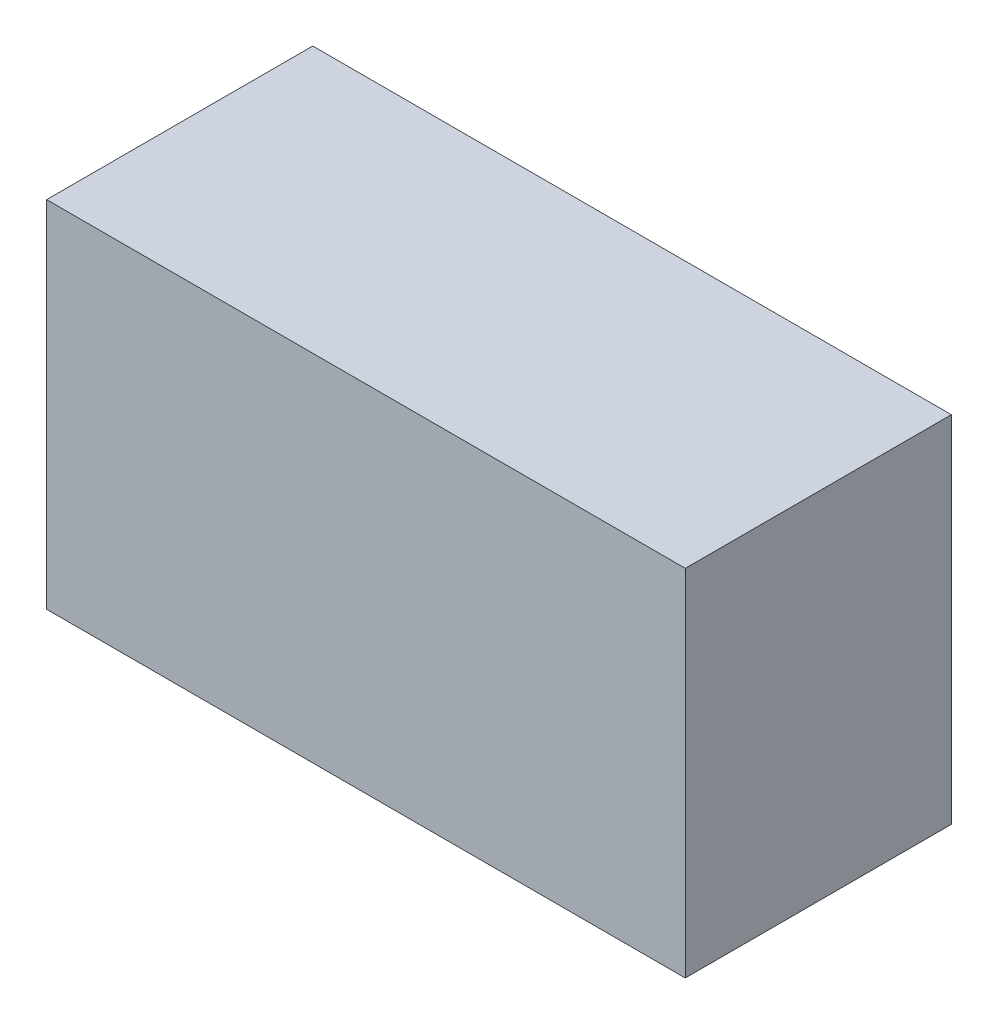
SolidWorks part; units mm, degrees
ref_plane "Front Plane" through (0, 0, 0) normal (0, 0, 1) x (1, 0, 0)
ref_plane "Top Plane" through (0, 0, 0) normal (0, 1, 0) x (1, 0, 0)
ref_plane "Right Plane" through (0, 0, 0) normal (1, 0, 0) x (0, 0, -1)
sketch "Sketch2" plane through (0, 0, 0) normal (0, 0, 1) x (1, 0, 0)
  line L1 (-16.3456, 9.7941) -> (19.6544, 9.7941)
  line L2 (-16.3456, 9.7941) -> (-16.3456, -10.2059)
  line L3 (-16.3456, -10.2059) -> (19.6544, -10.2059)
  line L4 (19.6544, 9.7941) -> (19.6544, -10.2059)
  dimension "D1" = 36
  dimension "D2" = 20
extrude "Boss-Extrude1" add sketch "Sketch2" along normal blind 15 contours L2 L1 L4 L3
